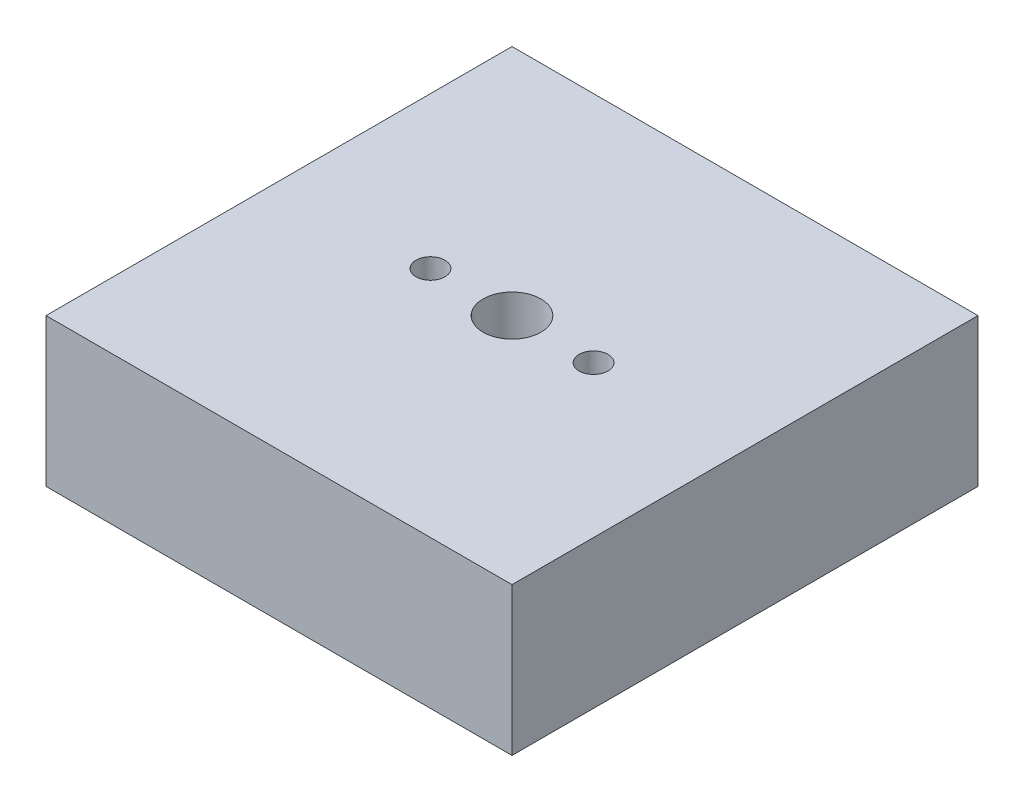
SolidWorks part; units mm, degrees
ref_plane "Front Plane" through (0, 0, 0) normal (0, 0, 1) x (1, 0, 0)
ref_plane "Top Plane" through (0, 0, 0) normal (0, 1, 0) x (1, 0, 0)
ref_plane "Right Plane" through (0, 0, 0) normal (1, 0, 0) x (0, 0, -1)
sketch "Sketch1" plane through (0, 0, 0) normal (0, 1, 0) x (1, 0, 0)
  line L0 (-5, -5) -> (5, -5)
  line L1 (-5, -5) -> (-5, 5)
  line L2 (5, -5) -> (5, 5)
  line L3 (-5, 5) -> (5, 5)
  line L4 (0, -5) -> (0, 5) construction
  line L6 (-5, 0) -> (5, 0) construction
  circle A0 centre (-1.75, 0) radius 0.31
  circle A1 centre (0, 0) radius 0.62
  circle A2 centre (1.75, 0) radius 0.31
  dimension "D5" = 0.62
  dimension "D9" = 1.24
  dimension "D10" = 0.62
  dimension "D2" = 10
  dimension "D3" = 1.75
  dimension "D4" = 1.75
  dimension "D7" = 10
extrude "Boss-Extrude1" add sketch "Sketch1" along normal blind 3.175
